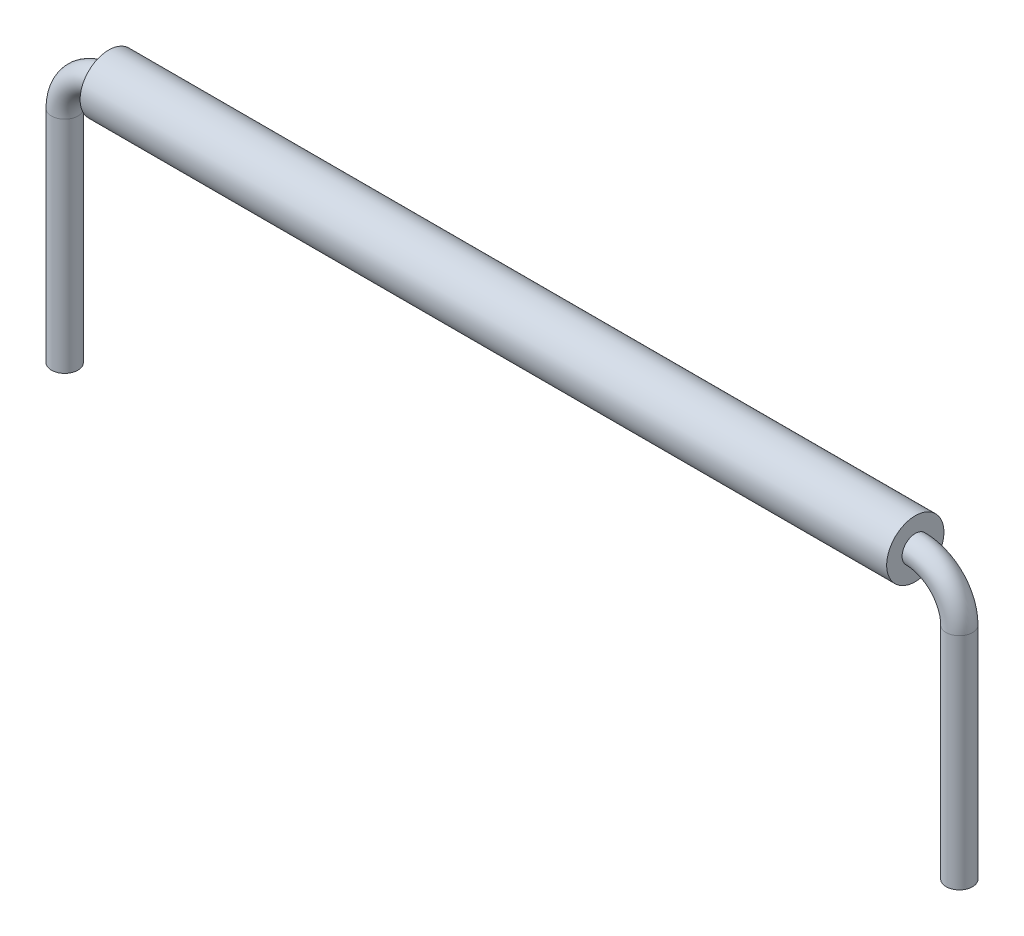
SolidWorks part; units mm, degrees
other "Insulation"
other "Wire"
ref_plane "Front Plane" through (0, 0, 0) normal (0, 0, 1) x (1, 0, 0)
ref_plane "Top Plane" through (0, 0, 0) normal (0, 1, 0) x (1, 0, 0)
ref_plane "Right Plane" through (0, 0, 0) normal (1, 0, 0) x (0, 0, -1)
sketch "Sketch1" plane through (0, 0, 0) normal (0, 0, 1) x (1, 0, 0)
  line L0 (-9.16, 0) -> (9.16, 0)
  line L1 (-10.16, -1) -> (-10.16, -6)
  line L2 (10.16, -1) -> (10.16, -6)
  line L3 (0, 0) -> (0, -6) construction
  line L4 (-10.16, -6) -> (10.16, -6) construction
  arc A0 (-9.16, 0) -> (-10.16, -1) centre (-9.16, -1) ccw
  arc A1 (9.16, 0) -> (10.16, -1) centre (9.16, -1) cw
  dimension "D1" = 1
  dimension "D2" = 20.32
  dimension "D3" = 6
sketch "Sketch2" plane through (0, 0, 0) normal (1, 0, 0) x (0, 0, -1)
  circle A0 centre (0, 0) radius 0.3
  dimension "D1" = 0.6
sweep "Sweep1" add profiles "Sketch2" path "Sketch1"
sketch "Sketch3" plane through (0, 0, 0) normal (1, 0, 0) x (0, 0, -1)
  circle A0 centre (0, 0) radius 0.65
  circle A1 centre (0, 0) radius 0.3
  dimension "D1" = 1.3
  dimension "D2" = 0.6
extrude "Boss-Extrude1" add sketch "Sketch3" along normal up to vertex (9.16 mm away) and the other way up to vertex (9.16 mm away) separate body up to point (9.16, 0, 0) other way up to point (-9.16, 0, 0)
